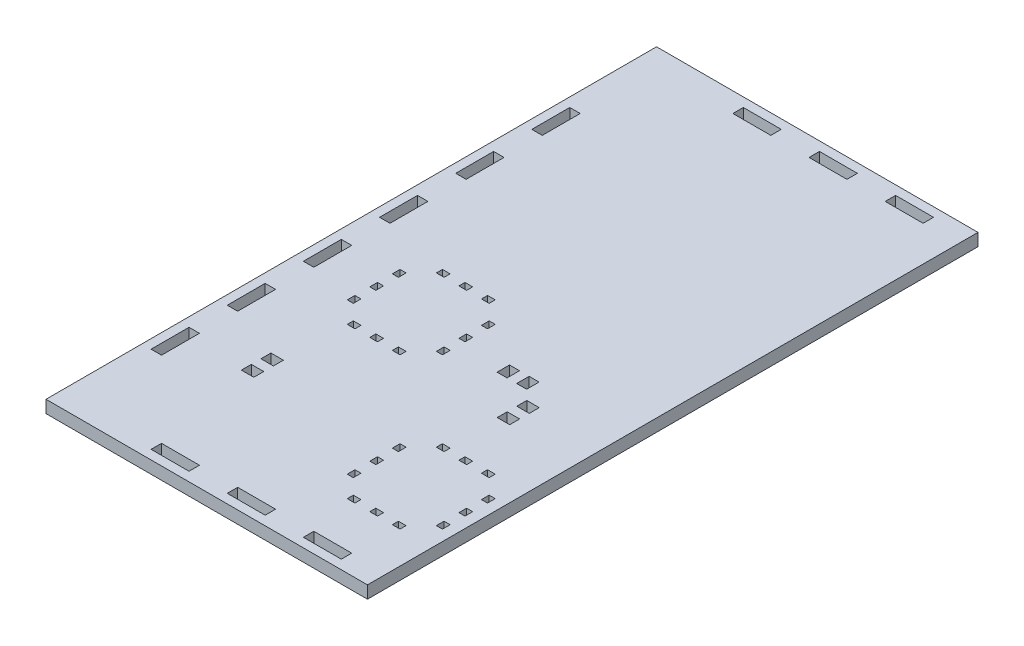
SolidWorks part; units mm, degrees
ref_plane "Front Plane" through (0, 0, 0) normal (0, 0, 1) x (1, 0, 0)
ref_plane "Top Plane" through (0, 0, 0) normal (0, 1, 0) x (1, 0, 0)
ref_plane "Right Plane" through (0, 0, 0) normal (1, 0, 0) x (0, 0, -1)
sketch "Sketch1" plane through (0, 0, 0) normal (0, 1, 0) x (1, 0, 0)
  line L182 (-7.5125, 303.9125) -> (303.8875, 303.9125)
  line L183 (-7.5125, 303.9125) -> (-7.5125, -7.4875)
  line L184 (-7.5125, -7.4875) -> (303.8875, -7.4875)
  line L185 (303.8875, 303.9125) -> (303.8875, -7.4875)
  line L195 (-2.9125, 60.7875) -> (2.4875, 60.7875)
  line L196 (-2.9125, 60.7875) -> (-2.9125, 41.3625)
  line L197 (-2.9125, 41.3625) -> (2.4875, 41.3625)
  line L198 (2.4875, 60.7875) -> (2.4875, 41.3625)
  line L200 (-2.9125, 99.6375) -> (2.4875, 99.6375)
  line L201 (-2.9125, 99.6375) -> (-2.9125, 80.2125)
  line L202 (-2.9125, 80.2125) -> (2.4875, 80.2125)
  line L203 (2.4875, 99.6375) -> (2.4875, 80.2125)
  line L205 (-2.9125, 138.4875) -> (2.4875, 138.4875)
  line L206 (-2.9125, 138.4875) -> (-2.9125, 119.0625)
  line L207 (-2.9125, 119.0625) -> (2.4875, 119.0625)
  line L208 (2.4875, 138.4875) -> (2.4875, 119.0625)
  line L211 (-2.9125, 177.3375) -> (2.4875, 177.3375)
  line L212 (-2.9125, 177.3375) -> (-2.9125, 157.9125)
  line L213 (-2.9125, 157.9125) -> (2.4875, 157.9125)
  line L214 (2.4875, 177.3375) -> (2.4875, 157.9125)
  line L216 (-2.9125, 216.1875) -> (2.4875, 216.1875)
  line L217 (-2.9125, 216.1875) -> (-2.9125, 196.7625)
  line L218 (-2.9125, 196.7625) -> (2.4875, 196.7625)
  line L219 (2.4875, 216.1875) -> (2.4875, 196.7625)
  line L221 (-2.9125, 255.0375) -> (2.4875, 255.0375)
  line L222 (-2.9125, 255.0375) -> (-2.9125, 235.6125)
  line L223 (-2.9125, 235.6125) -> (2.4875, 235.6125)
  line L224 (2.4875, 255.0375) -> (2.4875, 235.6125)
  line L236 (41.3625, 299.3125) -> (60.7875, 299.3125)
  line L237 (41.3625, 299.3125) -> (41.3625, 293.9125)
  line L238 (41.3625, 293.9125) -> (60.7875, 293.9125)
  line L239 (60.7875, 299.3125) -> (60.7875, 293.9125)
  line L241 (80.2125, 299.3125) -> (99.6375, 299.3125)
  line L242 (80.2125, 299.3125) -> (80.2125, 293.9125)
  line L243 (80.2125, 293.9125) -> (99.6375, 293.9125)
  line L244 (99.6375, 299.3125) -> (99.6375, 293.9125)
  line L246 (119.0625, 299.3125) -> (138.4875, 299.3125)
  line L247 (119.0625, 299.3125) -> (119.0625, 293.9125)
  line L248 (119.0625, 293.9125) -> (138.4875, 293.9125)
  line L249 (138.4875, 299.3125) -> (138.4875, 293.9125)
  line L251 (157.9125, 299.3125) -> (177.3375, 299.3125)
  line L252 (157.9125, 299.3125) -> (157.9125, 293.9125)
  line L253 (157.9125, 293.9125) -> (177.3375, 293.9125)
  line L254 (177.3375, 299.3125) -> (177.3375, 293.9125)
  line L256 (196.7625, 299.3125) -> (216.1875, 299.3125)
  line L257 (196.7625, 299.3125) -> (196.7625, 293.9125)
  line L258 (196.7625, 293.9125) -> (216.1875, 293.9125)
  line L259 (216.1875, 299.3125) -> (216.1875, 293.9125)
  line L260 (235.6125, 299.3125) -> (255.0375, 299.3125)
  line L261 (235.6125, 299.3125) -> (235.6125, 293.9125)
  line L262 (235.6125, 293.9125) -> (255.0375, 293.9125)
  line L263 (255.0375, 299.3125) -> (255.0375, 293.9125)
  line L272 (299.2875, 255.0625) -> (293.8875, 255.0625)
  line L273 (299.2875, 255.0625) -> (299.2875, 235.6375)
  line L274 (299.2875, 235.6375) -> (293.8875, 235.6375)
  line L275 (293.8875, 255.0625) -> (293.8875, 235.6375)
  line L276 (299.2875, 216.2125) -> (293.8875, 216.2125)
  line L277 (299.2875, 216.2125) -> (299.2875, 196.7875)
  line L278 (299.2875, 196.7875) -> (293.8875, 196.7875)
  line L279 (293.8875, 216.2125) -> (293.8875, 196.7875)
  line L280 (299.2875, 177.3625) -> (293.8875, 177.3625)
  line L281 (299.2875, 177.3625) -> (299.2875, 157.9375)
  line L282 (299.2875, 157.9375) -> (293.8875, 157.9375)
  line L283 (293.8875, 177.3625) -> (293.8875, 157.9375)
  line L284 (299.2875, 138.5125) -> (293.8875, 138.5125)
  line L285 (299.2875, 138.5125) -> (299.2875, 119.0875)
  line L286 (299.2875, 119.0875) -> (293.8875, 119.0875)
  line L287 (293.8875, 138.5125) -> (293.8875, 119.0875)
  line L288 (299.2875, 99.6625) -> (293.8875, 99.6625)
  line L289 (299.2875, 99.6625) -> (299.2875, 80.2375)
  line L290 (299.2875, 80.2375) -> (293.8875, 80.2375)
  line L291 (293.8875, 99.6625) -> (293.8875, 80.2375)
  line L292 (299.2875, 60.8125) -> (293.8875, 60.8125)
  line L293 (299.2875, 60.8125) -> (299.2875, 41.3875)
  line L294 (299.2875, 41.3875) -> (293.8875, 41.3875)
  line L295 (293.8875, 60.8125) -> (293.8875, 41.3875)
  line L304 (255.0125, 2.5125) -> (235.5875, 2.5125)
  line L305 (255.0125, 2.5125) -> (255.0125, -2.8875)
  line L306 (255.0125, -2.8875) -> (235.5875, -2.8875)
  line L307 (235.5875, 2.5125) -> (235.5875, -2.8875)
  line L308 (216.1625, 2.5125) -> (196.7375, 2.5125)
  line L309 (216.1625, 2.5125) -> (216.1625, -2.8875)
  line L310 (216.1625, -2.8875) -> (196.7375, -2.8875)
  line L311 (196.7375, 2.5125) -> (196.7375, -2.8875)
  line L312 (177.3125, 2.5125) -> (157.8875, 2.5125)
  line L313 (177.3125, 2.5125) -> (177.3125, -2.8875)
  line L314 (177.3125, -2.8875) -> (157.8875, -2.8875)
  line L315 (157.8875, 2.5125) -> (157.8875, -2.8875)
  line L316 (138.4625, 2.5125) -> (119.0375, 2.5125)
  line L317 (138.4625, 2.5125) -> (138.4625, -2.8875)
  line L318 (138.4625, -2.8875) -> (119.0375, -2.8875)
  line L319 (119.0375, 2.5125) -> (119.0375, -2.8875)
  line L320 (99.6125, 2.5125) -> (80.1875, 2.5125)
  line L321 (99.6125, 2.5125) -> (99.6125, -2.8875)
  line L322 (99.6125, -2.8875) -> (80.1875, -2.8875)
  line L323 (80.1875, 2.5125) -> (80.1875, -2.8875)
  line L324 (60.7625, 2.5125) -> (41.3375, 2.5125)
  line L325 (60.7625, 2.5125) -> (60.7625, -2.8875)
  line L326 (60.7625, -2.8875) -> (41.3375, -2.8875)
  line L327 (41.3375, 2.5125) -> (41.3375, -2.8875)
  line L528 (36.1625, 151.0125) -> (40.1625, 151.0125)
  line L529 (36.1625, 151.0125) -> (36.1625, 147.8375)
  line L530 (36.1625, 147.8375) -> (40.1625, 147.8375)
  line L531 (40.1625, 151.0125) -> (40.1625, 147.8375)
  line L532 (47.6625, 151.0125) -> (51.6625, 151.0125)
  line L533 (47.6625, 151.0125) -> (47.6625, 147.8375)
  line L534 (47.6625, 147.8375) -> (51.6625, 147.8375)
  line L535 (51.6625, 151.0125) -> (51.6625, 147.8375)
  line L536 (59.1625, 151.0125) -> (63.1625, 151.0125)
  line L537 (59.1625, 151.0125) -> (59.1625, 147.8375)
  line L538 (59.1625, 147.8375) -> (63.1625, 147.8375)
  line L539 (63.1625, 151.0125) -> (63.1625, 147.8375)
  line L540 (70.8125, 140.1875) -> (73.9875, 140.1875)
  line L541 (70.8125, 140.1875) -> (70.8125, 136.1875)
  line L542 (70.8125, 136.1875) -> (73.9875, 136.1875)
  line L543 (73.9875, 140.1875) -> (73.9875, 136.1875)
  line L544 (70.8125, 128.6875) -> (73.9875, 128.6875)
  line L545 (70.8125, 128.6875) -> (70.8125, 124.6875)
  line L546 (70.8125, 124.6875) -> (73.9875, 124.6875)
  line L547 (73.9875, 128.6875) -> (73.9875, 124.6875)
  line L548 (70.8125, 117.1875) -> (73.9875, 117.1875)
  line L549 (70.8125, 117.1875) -> (70.8125, 113.1875)
  line L550 (70.8125, 113.1875) -> (73.9875, 113.1875)
  line L551 (73.9875, 117.1875) -> (73.9875, 113.1875)
  line L552 (63.1625, 105.5375) -> (59.1625, 105.5375)
  line L553 (63.1625, 105.5375) -> (63.1625, 102.3625)
  line L554 (63.1625, 102.3625) -> (59.1625, 102.3625)
  line L555 (59.1625, 105.5375) -> (59.1625, 102.3625)
  line L556 (51.6625, 105.5375) -> (47.6625, 105.5375)
  line L557 (51.6625, 105.5375) -> (51.6625, 102.3625)
  line L558 (51.6625, 102.3625) -> (47.6625, 102.3625)
  line L559 (47.6625, 105.5375) -> (47.6625, 102.3625)
  line L560 (40.1625, 105.5375) -> (36.1625, 105.5375)
  line L561 (40.1625, 105.5375) -> (40.1625, 102.3625)
  line L562 (40.1625, 102.3625) -> (36.1625, 102.3625)
  line L563 (36.1625, 105.5375) -> (36.1625, 102.3625)
  line L564 (28.5125, 113.1875) -> (25.3375, 113.1875)
  line L565 (28.5125, 113.1875) -> (28.5125, 117.1875)
  line L566 (28.5125, 117.1875) -> (25.3375, 117.1875)
  line L567 (25.3375, 113.1875) -> (25.3375, 117.1875)
  line L568 (28.5125, 124.6875) -> (25.3375, 124.6875)
  line L569 (28.5125, 124.6875) -> (28.5125, 128.6875)
  line L570 (28.5125, 128.6875) -> (25.3375, 128.6875)
  line L571 (25.3375, 124.6875) -> (25.3375, 128.6875)
  line L572 (28.5125, 136.1875) -> (25.3375, 136.1875)
  line L573 (28.5125, 136.1875) -> (28.5125, 140.1875)
  line L574 (28.5125, 140.1875) -> (25.3375, 140.1875)
  line L575 (25.3375, 136.1875) -> (25.3375, 140.1875)
  line L576 (113.1625, 74.0125) -> (117.1625, 74.0125)
  line L577 (113.1625, 74.0125) -> (113.1625, 70.8375)
  line L578 (113.1625, 70.8375) -> (117.1625, 70.8375)
  line L579 (117.1625, 74.0125) -> (117.1625, 70.8375)
  line L580 (124.6625, 74.0125) -> (128.6625, 74.0125)
  line L581 (124.6625, 74.0125) -> (124.6625, 70.8375)
  line L582 (124.6625, 70.8375) -> (128.6625, 70.8375)
  line L583 (128.6625, 74.0125) -> (128.6625, 70.8375)
  line L584 (136.1625, 74.0125) -> (140.1625, 74.0125)
  line L585 (136.1625, 74.0125) -> (136.1625, 70.8375)
  line L586 (136.1625, 70.8375) -> (140.1625, 70.8375)
  line L587 (140.1625, 74.0125) -> (140.1625, 70.8375)
  line L588 (150.9875, 63.1875) -> (147.8125, 63.1875)
  line L589 (150.9875, 63.1875) -> (150.9875, 59.1875)
  line L590 (150.9875, 59.1875) -> (147.8125, 59.1875)
  line L591 (147.8125, 63.1875) -> (147.8125, 59.1875)
  line L592 (150.9875, 51.6875) -> (147.8125, 51.6875)
  line L593 (150.9875, 51.6875) -> (150.9875, 47.6875)
  line L594 (150.9875, 47.6875) -> (147.8125, 47.6875)
  line L595 (147.8125, 51.6875) -> (147.8125, 47.6875)
  line L596 (150.9875, 40.1875) -> (147.8125, 40.1875)
  line L597 (150.9875, 40.1875) -> (150.9875, 36.1875)
  line L598 (150.9875, 36.1875) -> (147.8125, 36.1875)
  line L599 (147.8125, 40.1875) -> (147.8125, 36.1875)
  line L600 (140.1625, 28.5375) -> (136.1625, 28.5375)
  line L601 (140.1625, 28.5375) -> (140.1625, 25.3625)
  line L602 (140.1625, 25.3625) -> (136.1625, 25.3625)
  line L603 (136.1625, 28.5375) -> (136.1625, 25.3625)
  line L604 (128.6625, 28.5375) -> (124.6625, 28.5375)
  line L605 (128.6625, 28.5375) -> (128.6625, 25.3625)
  line L606 (128.6625, 25.3625) -> (124.6625, 25.3625)
  line L607 (124.6625, 28.5375) -> (124.6625, 25.3625)
  line L608 (117.1625, 28.5375) -> (113.1625, 28.5375)
  line L609 (117.1625, 28.5375) -> (117.1625, 25.3625)
  line L610 (117.1625, 25.3625) -> (113.1625, 25.3625)
  line L611 (113.1625, 28.5375) -> (113.1625, 25.3625)
  line L612 (105.5125, 36.1875) -> (102.3375, 36.1875)
  line L613 (105.5125, 36.1875) -> (105.5125, 40.1875)
  line L614 (105.5125, 40.1875) -> (102.3375, 40.1875)
  line L615 (102.3375, 36.1875) -> (102.3375, 40.1875)
  line L616 (105.5125, 47.6875) -> (102.3375, 47.6875)
  line L617 (105.5125, 47.6875) -> (105.5125, 51.6875)
  line L618 (105.5125, 51.6875) -> (102.3375, 51.6875)
  line L619 (102.3375, 47.6875) -> (102.3375, 51.6875)
  line L620 (105.5125, 59.1875) -> (102.3375, 59.1875)
  line L621 (105.5125, 59.1875) -> (105.5125, 63.1875)
  line L622 (105.5125, 63.1875) -> (102.3375, 63.1875)
  line L623 (102.3375, 59.1875) -> (102.3375, 63.1875)
  dimension "D1" = 311.4
  dimension "D3" = 311.4
extrude "Boss-Extrude4" add sketch "Sketch1" along normal blind 6.35
sketch "Sketch4" plane through (0, 6.35, 0) normal (0, 1, 0) x (1, 0, 0)
  line L0 (303.8875, 303.9125) -> (-7.5125, 303.9125) construction
  line B0 (41.3375, 2.5125) -> (60.7625, 2.5125)
  line B1 (2.4875, 2.5125) -> (21.9125, 2.5125)
  line B2 (2.4875, 2.5125) -> (2.4875, -2.8875)
  line B3 (2.4875, -2.8875) -> (21.9125, -2.8875)
  line B4 (21.9125, 2.5125) -> (21.9125, -2.8875)
  line B5 (41.3375, 2.5125) -> (41.3375, -2.8875)
  line B6 (41.3375, -2.8875) -> (60.7625, -2.8875)
  line B7 (60.7625, 2.5125) -> (60.7625, -2.8875)
  line B8 (80.1875, 2.5125) -> (99.6125, 2.5125)
  line B9 (80.1875, 2.5125) -> (80.1875, -2.8875)
  line B10 (80.1875, -2.8875) -> (99.6125, -2.8875)
  line B11 (99.6125, 2.5125) -> (99.6125, -2.8875)
  line B12 (119.0375, 2.5125) -> (138.4625, 2.5125)
  line B13 (119.0375, 2.5125) -> (119.0375, -2.8875)
  line B14 (119.0375, -2.8875) -> (138.4625, -2.8875)
  line B15 (138.4625, 2.5125) -> (138.4625, -2.8875)
  line B16 (157.8875, 2.5125) -> (177.3125, 2.5125)
  line B17 (157.8875, 2.5125) -> (157.8875, -2.8875)
  line B18 (157.8875, -2.8875) -> (177.3125, -2.8875)
  line B19 (177.3125, 2.5125) -> (177.3125, -2.8875)
  line B20 (196.7375, 2.5125) -> (216.1625, 2.5125)
  line B21 (196.7375, 2.5125) -> (196.7375, -2.8875)
  line B22 (196.7375, -2.8875) -> (216.1625, -2.8875)
  line B23 (216.1625, 2.5125) -> (216.1625, -2.8875)
  line B24 (235.5875, 2.5125) -> (255.0125, 2.5125)
  line B25 (235.5875, 2.5125) -> (235.5875, -2.8875)
  line B26 (235.5875, -2.8875) -> (255.0125, -2.8875)
  line B27 (255.0125, 2.5125) -> (255.0125, -2.8875)
  line B28 (274.4375, 2.5125) -> (293.8625, 2.5125)
  line B29 (274.4375, 2.5125) -> (274.4375, -2.8875)
  line B30 (274.4375, -2.8875) -> (293.8625, -2.8875)
  line B31 (293.8625, 2.5125) -> (293.8625, -2.8875)
  line B32 (-2.9125, 60.7875) -> (2.4875, 60.7875)
  line B33 (-2.9125, 2.5125) -> (2.4875, 2.5125)
  line B34 (-2.9125, 2.5125) -> (-2.9125, 21.9375)
  line B35 (-2.9125, 21.9375) -> (2.4875, 21.9375)
  line B36 (2.4875, 2.5125) -> (2.4875, 21.9375)
  line B37 (2.4875, 41.3625) -> (2.4875, 60.7875)
  line B38 (-2.9125, 41.3625) -> (-2.9125, 60.7875)
  line B39 (-2.9125, 41.3625) -> (2.4875, 41.3625)
  line B40 (-2.9125, 99.6375) -> (2.4875, 99.6375)
  line B41 (2.4875, 80.2125) -> (2.4875, 99.6375)
  line B42 (-2.9125, 80.2125) -> (-2.9125, 99.6375)
  line B43 (-2.9125, 80.2125) -> (2.4875, 80.2125)
  line B44 (-2.9125, 138.4875) -> (2.4875, 138.4875)
  line B45 (2.4875, 119.0625) -> (2.4875, 138.4875)
  line B46 (-2.9125, 119.0625) -> (-2.9125, 138.4875)
  line B47 (-2.9125, 119.0625) -> (2.4875, 119.0625)
  line B48 (-2.9125, 177.3375) -> (2.4875, 177.3375)
  line B49 (2.4875, 157.9125) -> (2.4875, 177.3375)
  line B50 (-2.9125, 157.9125) -> (-2.9125, 177.3375)
  line B51 (-2.9125, 157.9125) -> (2.4875, 157.9125)
  line B52 (-2.9125, 216.1875) -> (2.4875, 216.1875)
  line B53 (2.4875, 196.7625) -> (2.4875, 216.1875)
  line B54 (-2.9125, 196.7625) -> (-2.9125, 216.1875)
  line B55 (-2.9125, 196.7625) -> (2.4875, 196.7625)
  line B56 (-2.9125, 255.0375) -> (2.4875, 255.0375)
  line B57 (2.4875, 235.6125) -> (2.4875, 255.0375)
  line B58 (-2.9125, 235.6125) -> (-2.9125, 255.0375)
  line B59 (-2.9125, 235.6125) -> (2.4875, 235.6125)
  line B60 (-2.9125, 293.8875) -> (2.4875, 293.8875)
  line B61 (2.4875, 274.4625) -> (2.4875, 293.8875)
  line B62 (-2.9125, 274.4625) -> (-2.9125, 293.8875)
  line B63 (-2.9125, 274.4625) -> (2.4875, 274.4625)
  line B64 (-7.5125, 303.9125) -> (303.8875, -7.4875) construction
  line B65 (21.9375, 299.3125) -> (21.9375, 293.9125)
  line B66 (21.9375, 299.3125) -> (2.5125, 299.3125)
  line B67 (21.9375, 293.9125) -> (2.5125, 293.9125)
  line B68 (2.5125, 299.3125) -> (2.5125, 293.9125)
  line B69 (60.7875, 299.3125) -> (60.7875, 293.9125)
  line B70 (60.7875, 299.3125) -> (41.3625, 299.3125)
  line B71 (60.7875, 293.9125) -> (41.3625, 293.9125)
  line B72 (41.3625, 299.3125) -> (41.3625, 293.9125)
  line B73 (99.6375, 299.3125) -> (99.6375, 293.9125)
  line B74 (99.6375, 299.3125) -> (80.2125, 299.3125)
  line B75 (99.6375, 293.9125) -> (80.2125, 293.9125)
  line B76 (80.2125, 299.3125) -> (80.2125, 293.9125)
  line B77 (138.4875, 299.3125) -> (138.4875, 293.9125)
  line B78 (138.4875, 299.3125) -> (119.0625, 299.3125)
  line B79 (138.4875, 293.9125) -> (119.0625, 293.9125)
  line B80 (119.0625, 299.3125) -> (119.0625, 293.9125)
  line B81 (177.3375, 299.3125) -> (177.3375, 293.9125)
  line B82 (177.3375, 299.3125) -> (157.9125, 299.3125)
  line B83 (177.3375, 293.9125) -> (157.9125, 293.9125)
  line B84 (157.9125, 299.3125) -> (157.9125, 293.9125)
  line B85 (216.1875, 299.3125) -> (216.1875, 293.9125)
  line B86 (216.1875, 299.3125) -> (196.7625, 299.3125)
  line B87 (216.1875, 293.9125) -> (196.7625, 293.9125)
  line B88 (196.7625, 299.3125) -> (196.7625, 293.9125)
  line B89 (255.0375, 299.3125) -> (255.0375, 293.9125)
  line B90 (255.0375, 299.3125) -> (235.6125, 299.3125)
  line B91 (255.0375, 293.9125) -> (235.6125, 293.9125)
  line B92 (293.8875, 293.9125) -> (274.4625, 293.9125)
  line B93 (274.4625, 299.3125) -> (274.4625, 293.9125)
  line B94 (293.8875, 299.3125) -> (274.4625, 299.3125)
  line B95 (293.8875, 299.3125) -> (293.8875, 293.9125)
  line B96 (235.6125, 299.3125) -> (235.6125, 293.9125)
  line B97 (293.8875, 2.5375) -> (299.2875, 2.5375)
  line B98 (299.2875, 21.9625) -> (299.2875, 2.5375)
  line B99 (293.8875, 21.9625) -> (299.2875, 21.9625)
  line B100 (293.8875, 21.9625) -> (293.8875, 2.5375)
  line B101 (293.8875, 41.3875) -> (299.2875, 41.3875)
  line B102 (299.2875, 60.8125) -> (299.2875, 41.3875)
  line B103 (293.8875, 60.8125) -> (299.2875, 60.8125)
  line B104 (293.8875, 60.8125) -> (293.8875, 41.3875)
  line B105 (293.8875, 80.2375) -> (299.2875, 80.2375)
  line B106 (299.2875, 99.6625) -> (299.2875, 80.2375)
  line B107 (293.8875, 99.6625) -> (299.2875, 99.6625)
  line B108 (293.8875, 99.6625) -> (293.8875, 80.2375)
  line B109 (293.8875, 119.0875) -> (299.2875, 119.0875)
  line B110 (299.2875, 138.5125) -> (299.2875, 119.0875)
  line B111 (293.8875, 138.5125) -> (299.2875, 138.5125)
  line B112 (293.8875, 138.5125) -> (293.8875, 119.0875)
  line B113 (293.8875, 157.9375) -> (299.2875, 157.9375)
  line B114 (299.2875, 177.3625) -> (299.2875, 157.9375)
  line B115 (293.8875, 177.3625) -> (299.2875, 177.3625)
  line B116 (293.8875, 177.3625) -> (293.8875, 157.9375)
  line B117 (293.8875, 196.7875) -> (299.2875, 196.7875)
  line B118 (299.2875, 216.2125) -> (299.2875, 196.7875)
  line B119 (293.8875, 216.2125) -> (299.2875, 216.2125)
  line B120 (293.8875, 216.2125) -> (293.8875, 196.7875)
  line B121 (293.8875, 235.6375) -> (299.2875, 235.6375)
  line B122 (299.2875, 255.0625) -> (299.2875, 235.6375)
  line B123 (293.8875, 255.0625) -> (299.2875, 255.0625)
  line B124 (293.8875, 274.4875) -> (299.2875, 274.4875)
  line B125 (299.2875, 293.9125) -> (299.2875, 274.4875)
  line B126 (293.8875, 293.9125) -> (299.2875, 293.9125)
  line B127 (293.8875, 293.9125) -> (293.8875, 274.4875)
  line B128 (293.8875, 255.0625) -> (293.8875, 235.6375)
  line B129 (2.5125, 293.9125) -> (2.4875, 293.8875)
  line B130 (293.8875, 2.5375) -> (293.8625, 2.5125)
  line B131 (35.6625, 260.7375) -> (115.6625, 260.7375)
  line B132 (35.6625, 260.7375) -> (35.6625, 180.7375)
  line B133 (35.6625, 180.7375) -> (115.6625, 180.7375)
  line B134 (115.6625, 260.7375) -> (115.6625, 180.7375)
  arc B135 (-2.9125, 293.8875) -> (2.5125, 299.2874) centre (2.4875, 293.8875) cw
  arc B136 (293.8625, -2.8875) -> (299.2624, 2.5375) centre (293.8625, 2.5125) ccw
  arc B137 (299.2875, 293.9125) -> (293.8875, 299.3125) centre (293.8875, 293.9125) ccw
  arc B138 (2.4875, -2.8875) -> (-2.9125, 2.5125) centre (2.4875, 2.5125) cw
sketch_block_instance "Outer Mounting Holes-4"
sketch_block "Outer Mounting Holes" parameters "D1"=5.4, "D2"=19.425, "D3"=19.425, "D4"=19.425, "D5"=80, "D6"=302.2
extrude "Cut-Extrude3" cut sketch "Sketch4" against normal blind 6.35 contours B66 B68 B67 B65 | B62 B63 B61 B60 | B135 B60 B129 B68 | B126 B137 B95 | B95 B94 B93 B92 | B126 B127 B124 B125 | B33 B36 B35 B34 | B4 B1 B2 B3 | B138 B2 B33 | B31 B136 B97 B130 | B31 B28 B29 B30 | B99 B100 B97 B98
sketch "Sketch5" plane through (0, 6.35, 0) normal (0, 1, 0) x (1, 0, 0)
  line L8 (254.9969, 293.9531) -> (254.9969, 299.2719)
  line L9 (235.6531, 293.9531) -> (254.9969, 293.9531)
  line L10 (235.6531, 299.2719) -> (235.6531, 293.9531)
  line L11 (254.9969, 299.2719) -> (235.6531, 299.2719)
  line L12 (254.9969, 293.9531) -> (254.9969, 299.2719)
  line L13 (235.6531, 293.9531) -> (254.9969, 293.9531)
  line L14 (235.6531, 299.2719) -> (235.6531, 293.9531)
  line L15 (254.9969, 299.2719) -> (235.6531, 299.2719)
  line L16 (-7.5531, -7.5281) -> (303.9281, -7.5281)
  line L17 (303.9281, -7.5281) -> (303.9281, 303.9531)
  line L18 (-7.5531, 303.9531) -> (-7.5531, -7.5281)
  line L19 (303.9281, 303.9531) -> (-7.5531, 303.9531)
  line L20 (-7.5531, -7.5281) -> (303.9281, -7.5281)
  line L21 (303.9281, -7.5281) -> (303.9281, 303.9531)
  line L22 (-7.5531, 303.9531) -> (-7.5531, -7.5281)
  line L23 (303.9281, 303.9531) -> (-7.5531, 303.9531)
  line L24 (293.8625, -2.8469) -> (274.4781, -2.8469)
  line L25 (274.4781, -2.8469) -> (274.4781, 2.4719)
  line L26 (274.4781, 2.4719) -> (293.8625, 2.4719)
  line L27 (293.8625, -2.8469) -> (274.4781, -2.8469)
  line L28 (274.5031, 299.2719) -> (293.8875, 299.2719)
  line L29 (274.5031, 293.9531) -> (274.5031, 299.2719)
  line L30 (293.8875, 293.9531) -> (274.5031, 293.9531)
  line L31 (274.5031, 299.2719) -> (293.8875, 299.2719)
  line L32 (274.5031, 293.9531) -> (274.5031, 299.2719)
  line L33 (293.8875, 293.9531) -> (274.5031, 293.9531)
  line L34 (299.2469, 41.4281) -> (299.2469, 60.7719)
  line L35 (293.9281, 196.8281) -> (299.2469, 196.8281)
  line L36 (293.9281, 216.1719) -> (293.9281, 196.8281)
  line L37 (299.2469, 196.8281) -> (299.2469, 216.1719)
  line L38 (299.2469, 216.1719) -> (293.9281, 216.1719)
  line L39 (293.9281, 196.8281) -> (299.2469, 196.8281)
  line L40 (293.9281, 274.5281) -> (299.2469, 274.5281)
  line L41 (299.2469, 274.5281) -> (299.2469, 293.9125)
  line L42 (293.9281, 293.9125) -> (293.9281, 274.5281)
  line L43 (293.9281, 274.5281) -> (299.2469, 274.5281)
  line L44 (299.2469, 274.5281) -> (299.2469, 293.9125)
  line L45 (293.9281, 293.9125) -> (293.9281, 274.5281)
  line L46 (293.9281, 216.1719) -> (293.9281, 196.8281)
  line L47 (299.2469, 196.8281) -> (299.2469, 216.1719)
  line L48 (299.2469, 216.1719) -> (293.9281, 216.1719)
  line L49 (293.9281, 41.4281) -> (299.2469, 41.4281)
  line L50 (293.9281, 60.7719) -> (293.9281, 41.4281)
  line L51 (299.2469, 60.7719) -> (293.9281, 60.7719)
  line L52 (299.2469, 41.4281) -> (299.2469, 60.7719)
  line L53 (293.9281, 41.4281) -> (299.2469, 41.4281)
  line L54 (293.9281, 60.7719) -> (293.9281, 41.4281)
  line L55 (299.2469, 60.7719) -> (293.9281, 60.7719)
  line L56 (274.4781, -2.8469) -> (274.4781, 2.4719)
  line L57 (293.9281, 235.6781) -> (299.2469, 235.6781)
  line L58 (299.2469, 235.6781) -> (299.2469, 255.0219)
  line L59 (299.2469, 255.0219) -> (293.9281, 255.0219)
  line L60 (293.9281, 255.0219) -> (293.9281, 235.6781)
  line L61 (293.9281, 235.6781) -> (299.2469, 235.6781)
  line L62 (299.2469, 235.6781) -> (299.2469, 255.0219)
  line L63 (299.2469, 255.0219) -> (293.9281, 255.0219)
  line L64 (293.9281, 255.0219) -> (293.9281, 235.6781)
  line L65 (274.4781, 2.4719) -> (293.8625, 2.4719)
  line L70 (299.2469, 157.9781) -> (299.2469, 177.3219)
  line L71 (293.9281, 177.3219) -> (293.9281, 157.9781)
  line L72 (293.9281, 157.9781) -> (299.2469, 157.9781)
  line L73 (21.8969, 293.9531) -> (21.8969, 299.2719)
  line L74 (2.5125, 293.9531) -> (21.8969, 293.9531)
  line L75 (21.8969, 299.2719) -> (2.5125, 299.2719)
  line L76 (21.8969, 293.9531) -> (21.8969, 299.2719)
  line L77 (2.5125, 293.9531) -> (21.8969, 293.9531)
  line L78 (21.8969, 299.2719) -> (2.5125, 299.2719)
  line L79 (299.2469, 177.3219) -> (293.9281, 177.3219)
  line L80 (299.2469, 157.9781) -> (299.2469, 177.3219)
  line L81 (293.9281, 177.3219) -> (293.9281, 157.9781)
  line L82 (293.9281, 157.9781) -> (299.2469, 157.9781)
  line L83 (299.2469, 177.3219) -> (293.9281, 177.3219)
  line L85 (-2.8719, 274.5031) -> (2.4469, 274.5031)
  line L86 (-2.8719, 293.8875) -> (-2.8719, 274.5031)
  line L87 (2.4469, 274.5031) -> (2.4469, 293.8875)
  line L88 (-2.8719, 274.5031) -> (2.4469, 274.5031)
  line L89 (-2.8719, 293.8875) -> (-2.8719, 274.5031)
  line L90 (2.4469, 274.5031) -> (2.4469, 293.8875)
  line L91 (-2.8719, 157.9531) -> (2.4469, 157.9531)
  line L92 (216.1219, -2.8469) -> (216.1219, 2.4719)
  line L93 (-2.8719, 177.2969) -> (-2.8719, 157.9531)
  line L94 (196.7781, 2.4719) -> (196.7781, -2.8469)
  line L95 (196.7781, -2.8469) -> (216.1219, -2.8469)
  line L96 (216.1219, 2.4719) -> (196.7781, 2.4719)
  line L97 (254.9719, -2.8469) -> (254.9719, 2.4719)
  line L98 (235.6281, 2.4719) -> (235.6281, -2.8469)
  line L99 (235.6281, -2.8469) -> (254.9719, -2.8469)
  line L100 (299.2469, 119.1281) -> (299.2469, 138.4719)
  line L101 (293.9281, 138.4719) -> (293.9281, 119.1281)
  line L102 (60.7469, 293.9531) -> (60.7469, 299.2719)
  line L103 (41.4031, 293.9531) -> (60.7469, 293.9531)
  line L104 (41.4031, 299.2719) -> (41.4031, 293.9531)
  line L105 (60.7469, 299.2719) -> (41.4031, 299.2719)
  line L106 (60.7469, 293.9531) -> (60.7469, 299.2719)
  line L107 (41.4031, 293.9531) -> (60.7469, 293.9531)
  line L108 (41.4031, 299.2719) -> (41.4031, 293.9531)
  line L109 (60.7469, 299.2719) -> (41.4031, 299.2719)
  line L110 (293.9281, 119.1281) -> (299.2469, 119.1281)
  line L111 (299.2469, 138.4719) -> (293.9281, 138.4719)
  line L112 (299.2469, 119.1281) -> (299.2469, 138.4719)
  line L113 (293.9281, 138.4719) -> (293.9281, 119.1281)
  line L114 (293.9281, 119.1281) -> (299.2469, 119.1281)
  line L115 (299.2469, 138.4719) -> (293.9281, 138.4719)
  line L116 (254.9719, 2.4719) -> (235.6281, 2.4719)
  line L117 (254.9719, -2.8469) -> (254.9719, 2.4719)
  line L118 (235.6281, 2.4719) -> (235.6281, -2.8469)
  line L119 (235.6281, -2.8469) -> (254.9719, -2.8469)
  line L120 (254.9719, 2.4719) -> (235.6281, 2.4719)
  line L121 (216.1219, -2.8469) -> (216.1219, 2.4719)
  line L122 (196.7781, 2.4719) -> (196.7781, -2.8469)
  line L123 (196.7781, -2.8469) -> (216.1219, -2.8469)
  line L124 (99.5969, 293.9531) -> (99.5969, 299.2719)
  line L125 (80.2531, 299.2719) -> (80.2531, 293.9531)
  line L126 (80.2531, 293.9531) -> (99.5969, 293.9531)
  line L127 (99.5969, 299.2719) -> (80.2531, 299.2719)
  line L128 (99.5969, 293.9531) -> (99.5969, 299.2719)
  line L129 (80.2531, 299.2719) -> (80.2531, 293.9531)
  line L130 (80.2531, 293.9531) -> (99.5969, 293.9531)
  line L131 (99.5969, 299.2719) -> (80.2531, 299.2719)
  line L132 (216.1219, 2.4719) -> (196.7781, 2.4719)
  line L133 (2.4469, 157.9531) -> (2.4469, 177.2969)
  line L134 (299.2469, 80.2781) -> (299.2469, 99.6219)
  line L135 (293.9281, 80.2781) -> (299.2469, 80.2781)
  line L136 (293.9281, 99.6219) -> (293.9281, 80.2781)
  line L137 (299.2469, 99.6219) -> (293.9281, 99.6219)
  line L138 (299.2469, 80.2781) -> (299.2469, 99.6219)
  line L139 (293.9281, 80.2781) -> (299.2469, 80.2781)
  line L140 (293.9281, 99.6219) -> (293.9281, 80.2781)
  line L141 (299.2469, 99.6219) -> (293.9281, 99.6219)
  line L142 (119.1031, 299.2719) -> (119.1031, 293.9531)
  line L143 (138.4469, 293.9531) -> (138.4469, 299.2719)
  line L144 (119.1031, 293.9531) -> (138.4469, 293.9531)
  line L145 (138.4469, 299.2719) -> (119.1031, 299.2719)
  line L146 (119.1031, 299.2719) -> (119.1031, 293.9531)
  line L147 (138.4469, 293.9531) -> (138.4469, 299.2719)
  line L148 (119.1031, 293.9531) -> (138.4469, 293.9531)
  line L149 (138.4469, 299.2719) -> (119.1031, 299.2719)
  line L150 (2.4469, 177.2969) -> (-2.8719, 177.2969)
  line L151 (-2.8719, 157.9531) -> (2.4469, 157.9531)
  line L152 (-2.8719, 177.2969) -> (-2.8719, 157.9531)
  line L153 (2.4469, 157.9531) -> (2.4469, 177.2969)
  line L154 (2.4469, 177.2969) -> (-2.8719, 177.2969)
  line L155 (-2.8719, 235.6531) -> (2.4469, 235.6531)
  line L156 (2.4469, 235.6531) -> (2.4469, 254.9969)
  line L157 (-2.8719, 254.9969) -> (-2.8719, 235.6531)
  line L158 (2.4469, 254.9969) -> (-2.8719, 254.9969)
  line L159 (177.2719, -2.8469) -> (177.2719, 2.4719)
  line L160 (157.9531, 299.2719) -> (157.9531, 293.9531)
  line L161 (177.2969, 293.9531) -> (177.2969, 299.2719)
  line L162 (157.9531, 293.9531) -> (177.2969, 293.9531)
  line L163 (177.2969, 299.2719) -> (157.9531, 299.2719)
  line L164 (157.9531, 299.2719) -> (157.9531, 293.9531)
  line L165 (177.2969, 293.9531) -> (177.2969, 299.2719)
  line L166 (157.9531, 293.9531) -> (177.2969, 293.9531)
  line L167 (177.2969, 299.2719) -> (157.9531, 299.2719)
  line L168 (157.9281, 2.4719) -> (157.9281, -2.8469)
  line L169 (157.9281, -2.8469) -> (177.2719, -2.8469)
  line L170 (299.2469, 2.5375) -> (299.2469, 21.9219)
  line L171 (299.2469, 21.9219) -> (293.9281, 21.9219)
  line L172 (293.9281, 21.9219) -> (293.9281, 2.5375)
  line L173 (299.2469, 2.5375) -> (299.2469, 21.9219)
  line L174 (299.2469, 21.9219) -> (293.9281, 21.9219)
  line L175 (293.9281, 21.9219) -> (293.9281, 2.5375)
  line L176 (177.2719, 2.4719) -> (157.9281, 2.4719)
  line L177 (177.2719, -2.8469) -> (177.2719, 2.4719)
  line L178 (157.9281, 2.4719) -> (157.9281, -2.8469)
  line L179 (157.9281, -2.8469) -> (177.2719, -2.8469)
  line L180 (196.8031, 299.2719) -> (196.8031, 293.9531)
  line L181 (216.1469, 293.9531) -> (216.1469, 299.2719)
  line L182 (216.1469, 299.2719) -> (196.8031, 299.2719)
  line L183 (196.8031, 293.9531) -> (216.1469, 293.9531)
  line L184 (196.8031, 299.2719) -> (196.8031, 293.9531)
  line L185 (216.1469, 293.9531) -> (216.1469, 299.2719)
  line L186 (216.1469, 299.2719) -> (196.8031, 299.2719)
  line L187 (196.8031, 293.9531) -> (216.1469, 293.9531)
  line L188 (177.2719, 2.4719) -> (157.9281, 2.4719)
  line L189 (-2.8719, 235.6531) -> (2.4469, 235.6531)
  line L190 (2.4469, 235.6531) -> (2.4469, 254.9969)
  line L194 (-2.8719, 254.9969) -> (-2.8719, 235.6531)
  line L195 (-2.8719, 196.8031) -> (2.4469, 196.8031)
  line L196 (2.4469, 196.8031) -> (2.4469, 216.1469)
  line L197 (-2.8719, 216.1469) -> (-2.8719, 196.8031)
  line L198 (2.4469, 216.1469) -> (-2.8719, 216.1469)
  line L199 (138.4219, 2.4719) -> (119.0781, 2.4719)
  line L200 (119.0781, -2.8469) -> (138.4219, -2.8469)
  line L201 (138.4219, -2.8469) -> (138.4219, 2.4719)
  line L202 (119.0781, 2.4719) -> (119.0781, -2.8469)
  line L203 (138.4219, 2.4719) -> (119.0781, 2.4719)
  line L204 (119.0781, -2.8469) -> (138.4219, -2.8469)
  line L205 (138.4219, -2.8469) -> (138.4219, 2.4719)
  line L206 (119.0781, 2.4719) -> (119.0781, -2.8469)
  line L207 (-2.8719, 196.8031) -> (2.4469, 196.8031)
  line L208 (2.4469, 196.8031) -> (2.4469, 216.1469)
  line L209 (-2.8719, 216.1469) -> (-2.8719, 196.8031)
  line L210 (2.4469, 216.1469) -> (-2.8719, 216.1469)
  line L211 (2.4469, 254.9969) -> (-2.8719, 254.9969)
  line L212 (51.6219, 147.8781) -> (51.6219, 150.9719)
  line L213 (47.7031, 147.8781) -> (51.6219, 147.8781)
  line L214 (47.7031, 150.9719) -> (47.7031, 147.8781)
  line L215 (51.6219, 150.9719) -> (47.7031, 150.9719)
  line L216 (51.6219, 147.8781) -> (51.6219, 150.9719)
  line L217 (80.2281, 2.4719) -> (80.2281, -2.8469)
  line L218 (99.5719, -2.8469) -> (99.5719, 2.4719)
  line L219 (80.2281, -2.8469) -> (99.5719, -2.8469)
  line L220 (99.5719, 2.4719) -> (80.2281, 2.4719)
  line L221 (80.2281, 2.4719) -> (80.2281, -2.8469)
  line L222 (99.5719, -2.8469) -> (99.5719, 2.4719)
  line L223 (80.2281, -2.8469) -> (99.5719, -2.8469)
  line L224 (99.5719, 2.4719) -> (80.2281, 2.4719)
  line L225 (47.7031, 147.8781) -> (51.6219, 147.8781)
  line L226 (47.7031, 150.9719) -> (47.7031, 147.8781)
  line L227 (51.6219, 150.9719) -> (47.7031, 150.9719)
  line L228 (63.1219, 147.8781) -> (63.1219, 150.9719)
  line L229 (59.2031, 147.8781) -> (63.1219, 147.8781)
  line L230 (59.2031, 150.9719) -> (59.2031, 147.8781)
  line L231 (63.1219, 150.9719) -> (59.2031, 150.9719)
  line L232 (63.1219, 147.8781) -> (63.1219, 150.9719)
  line L233 (59.2031, 147.8781) -> (63.1219, 147.8781)
  line L234 (59.2031, 150.9719) -> (59.2031, 147.8781)
  line L235 (41.3781, 2.4719) -> (41.3781, -2.8469)
  line L236 (60.7219, -2.8469) -> (60.7219, 2.4719)
  line L237 (41.3781, -2.8469) -> (60.7219, -2.8469)
  line L238 (60.7219, 2.4719) -> (41.3781, 2.4719)
  line L239 (41.3781, 2.4719) -> (41.3781, -2.8469)
  line L240 (60.7219, -2.8469) -> (60.7219, 2.4719)
  line L241 (41.3781, -2.8469) -> (60.7219, -2.8469)
  line L242 (60.7219, 2.4719) -> (41.3781, 2.4719)
  line L243 (63.1219, 150.9719) -> (59.2031, 150.9719)
  line L248 (21.8719, 2.4719) -> (21.8719, -2.8469)
  line L249 (21.8719, -2.8469) -> (2.4875, -2.8469)
  line L250 (2.4875, 2.4719) -> (21.8719, 2.4719)
  line L251 (21.8719, 2.4719) -> (21.8719, -2.8469)
  line L252 (21.8719, -2.8469) -> (2.4875, -2.8469)
  line L253 (2.4875, 2.4719) -> (21.8719, 2.4719)
  line L260 (2.4469, 21.8969) -> (2.4469, 2.5125)
  line L261 (-2.8719, 2.5125) -> (-2.8719, 21.8969)
  line L262 (-2.8719, 21.8969) -> (2.4469, 21.8969)
  line L263 (2.4469, 21.8969) -> (2.4469, 2.5125)
  line L264 (-2.8719, 2.5125) -> (-2.8719, 21.8969)
  line L265 (-2.8719, 21.8969) -> (2.4469, 21.8969)
  line L266 (40.1219, 147.8781) -> (40.1219, 150.9719)
  line L267 (36.2031, 147.8781) -> (40.1219, 147.8781)
  line L268 (36.2031, 150.9719) -> (36.2031, 147.8781)
  line L269 (40.1219, 150.9719) -> (36.2031, 150.9719)
  line L270 (40.1219, 147.8781) -> (40.1219, 150.9719)
  line L271 (36.2031, 147.8781) -> (40.1219, 147.8781)
  line L272 (36.2031, 150.9719) -> (36.2031, 147.8781)
  line L273 (40.1219, 150.9719) -> (36.2031, 150.9719)
  line L277 (-2.8719, 41.4031) -> (2.4469, 41.4031)
  line L278 (2.4469, 41.4031) -> (2.4469, 60.7469)
  line L279 (-2.8719, 60.7469) -> (-2.8719, 41.4031)
  line L280 (2.4469, 60.7469) -> (-2.8719, 60.7469)
  line L281 (-2.8719, 41.4031) -> (2.4469, 41.4031)
  line L282 (2.4469, 41.4031) -> (2.4469, 60.7469)
  line L283 (-2.8719, 60.7469) -> (-2.8719, 41.4031)
  line L284 (2.4469, 60.7469) -> (-2.8719, 60.7469)
  line L292 (28.4719, 136.2281) -> (28.4719, 140.1469)
  line L293 (25.3781, 140.1469) -> (25.3781, 136.2281)
  line L294 (25.3781, 136.2281) -> (28.4719, 136.2281)
  line L295 (-2.8719, 80.2531) -> (2.4469, 80.2531)
  line L296 (-2.8719, 99.5969) -> (-2.8719, 80.2531)
  line L297 (2.4469, 80.2531) -> (2.4469, 99.5969)
  line L298 (2.4469, 99.5969) -> (-2.8719, 99.5969)
  line L299 (-2.8719, 80.2531) -> (2.4469, 80.2531)
  line L300 (-2.8719, 99.5969) -> (-2.8719, 80.2531)
  line L301 (2.4469, 80.2531) -> (2.4469, 99.5969)
  line L302 (2.4469, 99.5969) -> (-2.8719, 99.5969)
  line L303 (28.4719, 140.1469) -> (25.3781, 140.1469)
  line L304 (28.4719, 136.2281) -> (28.4719, 140.1469)
  line L305 (25.3781, 140.1469) -> (25.3781, 136.2281)
  line L306 (25.3781, 136.2281) -> (28.4719, 136.2281)
  line L307 (28.4719, 140.1469) -> (25.3781, 140.1469)
  line L313 (-2.8719, 119.1031) -> (2.4469, 119.1031)
  line L314 (2.4469, 119.1031) -> (2.4469, 138.4469)
  line L315 (-2.8719, 138.4469) -> (-2.8719, 119.1031)
  line L316 (2.4469, 138.4469) -> (-2.8719, 138.4469)
  line L317 (-2.8719, 119.1031) -> (2.4469, 119.1031)
  line L318 (2.4469, 119.1031) -> (2.4469, 138.4469)
  line L319 (-2.8719, 138.4469) -> (-2.8719, 119.1031)
  line L320 (2.4469, 138.4469) -> (-2.8719, 138.4469)
  line L326 (28.4719, 124.7281) -> (28.4719, 128.6469)
  line L327 (25.3781, 128.6469) -> (25.3781, 124.7281)
  line L328 (25.3781, 124.7281) -> (28.4719, 124.7281)
  line L329 (28.4719, 128.6469) -> (25.3781, 128.6469)
  line L330 (28.4719, 124.7281) -> (28.4719, 128.6469)
  line L331 (25.3781, 128.6469) -> (25.3781, 124.7281)
  line L332 (25.3781, 124.7281) -> (28.4719, 124.7281)
  line L333 (28.4719, 128.6469) -> (25.3781, 128.6469)
  line L344 (28.4719, 113.2281) -> (28.4719, 117.1469)
  line L345 (25.3781, 117.1469) -> (25.3781, 113.2281)
  line L346 (25.3781, 113.2281) -> (28.4719, 113.2281)
  line L347 (28.4719, 117.1469) -> (25.3781, 117.1469)
  line L348 (28.4719, 113.2281) -> (28.4719, 117.1469)
  line L349 (25.3781, 117.1469) -> (25.3781, 113.2281)
  line L350 (25.3781, 113.2281) -> (28.4719, 113.2281)
  line L351 (28.4719, 117.1469) -> (25.3781, 117.1469)
  line L362 (40.1219, 102.4031) -> (40.1219, 105.4969)
  line L363 (36.2031, 105.4969) -> (36.2031, 102.4031)
  line L364 (36.2031, 102.4031) -> (40.1219, 102.4031)
  line L365 (40.1219, 105.4969) -> (36.2031, 105.4969)
  line L366 (40.1219, 102.4031) -> (40.1219, 105.4969)
  line L367 (36.2031, 105.4969) -> (36.2031, 102.4031)
  line L368 (36.2031, 102.4031) -> (40.1219, 102.4031)
  line L369 (40.1219, 105.4969) -> (36.2031, 105.4969)
  line L380 (51.6219, 102.4031) -> (51.6219, 105.4969)
  line L381 (47.7031, 105.4969) -> (47.7031, 102.4031)
  line L382 (51.6219, 105.4969) -> (47.7031, 105.4969)
  line L383 (47.7031, 102.4031) -> (51.6219, 102.4031)
  line L384 (51.6219, 102.4031) -> (51.6219, 105.4969)
  line L385 (47.7031, 105.4969) -> (47.7031, 102.4031)
  line L386 (51.6219, 105.4969) -> (47.7031, 105.4969)
  line L387 (47.7031, 102.4031) -> (51.6219, 102.4031)
  line L398 (63.1219, 102.4031) -> (63.1219, 105.4969)
  line L399 (59.2031, 105.4969) -> (59.2031, 102.4031)
  line L400 (59.2031, 102.4031) -> (63.1219, 102.4031)
  line L401 (63.1219, 105.4969) -> (59.2031, 105.4969)
  line L402 (63.1219, 102.4031) -> (63.1219, 105.4969)
  line L403 (59.2031, 105.4969) -> (59.2031, 102.4031)
  line L404 (59.2031, 102.4031) -> (63.1219, 102.4031)
  line L405 (63.1219, 105.4969) -> (59.2031, 105.4969)
  line L416 (73.9469, 136.2281) -> (73.9469, 140.1469)
  line L417 (70.8531, 136.2281) -> (73.9469, 136.2281)
  line L418 (70.8531, 140.1469) -> (70.8531, 136.2281)
  line L419 (73.9469, 140.1469) -> (70.8531, 140.1469)
  line L420 (73.9469, 136.2281) -> (73.9469, 140.1469)
  line L421 (70.8531, 136.2281) -> (73.9469, 136.2281)
  line L422 (70.8531, 140.1469) -> (70.8531, 136.2281)
  line L423 (73.9469, 140.1469) -> (70.8531, 140.1469)
  line L434 (73.9469, 124.7281) -> (73.9469, 128.6469)
  line L435 (70.8531, 124.7281) -> (73.9469, 124.7281)
  line L436 (70.8531, 128.6469) -> (70.8531, 124.7281)
  line L437 (73.9469, 128.6469) -> (70.8531, 128.6469)
  line L438 (73.9469, 124.7281) -> (73.9469, 128.6469)
  line L439 (70.8531, 124.7281) -> (73.9469, 124.7281)
  line L440 (70.8531, 128.6469) -> (70.8531, 124.7281)
  line L441 (73.9469, 128.6469) -> (70.8531, 128.6469)
  line L456 (73.9469, 113.2281) -> (73.9469, 117.1469)
  line L457 (70.8531, 113.2281) -> (73.9469, 113.2281)
  line L458 (70.8531, 117.1469) -> (70.8531, 113.2281)
  line L459 (73.9469, 117.1469) -> (70.8531, 117.1469)
  line L460 (73.9469, 113.2281) -> (73.9469, 117.1469)
  line L461 (70.8531, 113.2281) -> (73.9469, 113.2281)
  line L462 (70.8531, 117.1469) -> (70.8531, 113.2281)
  line L463 (73.9469, 117.1469) -> (70.8531, 117.1469)
  line L474 (128.6219, 70.8781) -> (128.6219, 73.9719)
  line L475 (124.7031, 73.9719) -> (124.7031, 70.8781)
  line L476 (124.7031, 70.8781) -> (128.6219, 70.8781)
  line L477 (128.6219, 73.9719) -> (124.7031, 73.9719)
  line L478 (128.6219, 70.8781) -> (128.6219, 73.9719)
  line L479 (124.7031, 73.9719) -> (124.7031, 70.8781)
  line L480 (124.7031, 70.8781) -> (128.6219, 70.8781)
  line L481 (128.6219, 73.9719) -> (124.7031, 73.9719)
  line L492 (113.2031, 73.9719) -> (113.2031, 70.8781)
  line L493 (117.1219, 70.8781) -> (117.1219, 73.9719)
  line L494 (113.2031, 70.8781) -> (117.1219, 70.8781)
  line L495 (117.1219, 73.9719) -> (113.2031, 73.9719)
  line L496 (113.2031, 73.9719) -> (113.2031, 70.8781)
  line L497 (117.1219, 70.8781) -> (117.1219, 73.9719)
  line L498 (113.2031, 70.8781) -> (117.1219, 70.8781)
  line L499 (117.1219, 73.9719) -> (113.2031, 73.9719)
  line L510 (140.1219, 70.8781) -> (140.1219, 73.9719)
  line L511 (136.2031, 73.9719) -> (136.2031, 70.8781)
  line L512 (136.2031, 70.8781) -> (140.1219, 70.8781)
  line L513 (140.1219, 73.9719) -> (136.2031, 73.9719)
  line L514 (140.1219, 70.8781) -> (140.1219, 73.9719)
  line L515 (136.2031, 73.9719) -> (136.2031, 70.8781)
  line L516 (136.2031, 70.8781) -> (140.1219, 70.8781)
  line L517 (140.1219, 73.9719) -> (136.2031, 73.9719)
  line L528 (150.9469, 59.2281) -> (150.9469, 63.1469)
  line L529 (147.8531, 63.1469) -> (147.8531, 59.2281)
  line L530 (147.8531, 59.2281) -> (150.9469, 59.2281)
  line L531 (150.9469, 63.1469) -> (147.8531, 63.1469)
  line L532 (150.9469, 59.2281) -> (150.9469, 63.1469)
  line L533 (147.8531, 63.1469) -> (147.8531, 59.2281)
  line L534 (147.8531, 59.2281) -> (150.9469, 59.2281)
  line L535 (150.9469, 63.1469) -> (147.8531, 63.1469)
  line L546 (150.9469, 47.7281) -> (150.9469, 51.6469)
  line L547 (147.8531, 51.6469) -> (147.8531, 47.7281)
  line L548 (147.8531, 47.7281) -> (150.9469, 47.7281)
  line L549 (150.9469, 51.6469) -> (147.8531, 51.6469)
  line L550 (150.9469, 47.7281) -> (150.9469, 51.6469)
  line L551 (147.8531, 51.6469) -> (147.8531, 47.7281)
  line L552 (147.8531, 47.7281) -> (150.9469, 47.7281)
  line L553 (150.9469, 51.6469) -> (147.8531, 51.6469)
  line L564 (147.8531, 40.1469) -> (147.8531, 36.2281)
  line L565 (150.9469, 36.2281) -> (150.9469, 40.1469)
  line L566 (147.8531, 36.2281) -> (150.9469, 36.2281)
  line L567 (150.9469, 40.1469) -> (147.8531, 40.1469)
  line L568 (147.8531, 40.1469) -> (147.8531, 36.2281)
  line L569 (150.9469, 36.2281) -> (150.9469, 40.1469)
  line L570 (147.8531, 36.2281) -> (150.9469, 36.2281)
  line L571 (150.9469, 40.1469) -> (147.8531, 40.1469)
  line L582 (140.1219, 25.4031) -> (140.1219, 28.4969)
  line L583 (136.2031, 25.4031) -> (140.1219, 25.4031)
  line L584 (136.2031, 28.4969) -> (136.2031, 25.4031)
  line L585 (140.1219, 28.4969) -> (136.2031, 28.4969)
  line L586 (140.1219, 25.4031) -> (140.1219, 28.4969)
  line L587 (136.2031, 25.4031) -> (140.1219, 25.4031)
  line L588 (136.2031, 28.4969) -> (136.2031, 25.4031)
  line L589 (140.1219, 28.4969) -> (136.2031, 28.4969)
  line L600 (128.6219, 25.4031) -> (128.6219, 28.4969)
  line L601 (124.7031, 28.4969) -> (124.7031, 25.4031)
  line L602 (124.7031, 25.4031) -> (128.6219, 25.4031)
  line L603 (128.6219, 28.4969) -> (124.7031, 28.4969)
  line L604 (128.6219, 25.4031) -> (128.6219, 28.4969)
  line L605 (124.7031, 28.4969) -> (124.7031, 25.4031)
  line L606 (124.7031, 25.4031) -> (128.6219, 25.4031)
  line L607 (128.6219, 28.4969) -> (124.7031, 28.4969)
  line L618 (113.2031, 28.4969) -> (113.2031, 25.4031)
  line L619 (117.1219, 25.4031) -> (117.1219, 28.4969)
  line L620 (113.2031, 25.4031) -> (117.1219, 25.4031)
  line L621 (117.1219, 28.4969) -> (113.2031, 28.4969)
  line L622 (113.2031, 28.4969) -> (113.2031, 25.4031)
  line L623 (117.1219, 25.4031) -> (117.1219, 28.4969)
  line L624 (113.2031, 25.4031) -> (117.1219, 25.4031)
  line L625 (117.1219, 28.4969) -> (113.2031, 28.4969)
  line L636 (105.4719, 36.2281) -> (105.4719, 40.1469)
  line L637 (102.3781, 40.1469) -> (102.3781, 36.2281)
  line L638 (102.3781, 36.2281) -> (105.4719, 36.2281)
  line L639 (105.4719, 40.1469) -> (102.3781, 40.1469)
  line L640 (105.4719, 36.2281) -> (105.4719, 40.1469)
  line L641 (102.3781, 40.1469) -> (102.3781, 36.2281)
  line L642 (102.3781, 36.2281) -> (105.4719, 36.2281)
  line L643 (105.4719, 40.1469) -> (102.3781, 40.1469)
  line L654 (102.3781, 51.6469) -> (102.3781, 47.7281)
  line L655 (105.4719, 47.7281) -> (105.4719, 51.6469)
  line L656 (102.3781, 47.7281) -> (105.4719, 47.7281)
  line L657 (105.4719, 51.6469) -> (102.3781, 51.6469)
  line L658 (102.3781, 51.6469) -> (102.3781, 47.7281)
  line L659 (105.4719, 47.7281) -> (105.4719, 51.6469)
  line L660 (102.3781, 47.7281) -> (105.4719, 47.7281)
  line L661 (105.4719, 51.6469) -> (102.3781, 51.6469)
  line L672 (105.4719, 59.2281) -> (105.4719, 63.1469)
  line L673 (102.3781, 63.1469) -> (102.3781, 59.2281)
  line L674 (102.3781, 59.2281) -> (105.4719, 59.2281)
  line L675 (105.4719, 63.1469) -> (102.3781, 63.1469)
  line L676 (105.4719, 59.2281) -> (105.4719, 63.1469)
  line L677 (102.3781, 63.1469) -> (102.3781, 59.2281)
  line L678 (102.3781, 59.2281) -> (105.4719, 59.2281)
  line L679 (105.4719, 63.1469) -> (102.3781, 63.1469)
  arc A2 (299.2469, 293.9125) -> (293.8875, 299.2719) centre (293.8875, 293.9125) ccw
  arc A3 (299.2469, 293.9125) -> (293.8875, 299.2719) centre (293.8875, 293.9125) ccw
  arc A4 (293.8625, -2.8469) -> (299.2218, 2.5373) centre (293.8625, 2.5125) ccw
  arc A5 (293.8625, -2.8469) -> (299.2218, 2.5373) centre (293.8625, 2.5125) ccw
  arc A6 (-2.8719, 2.5125) -> (2.4875, -2.8469) centre (2.4875, 2.5125) ccw
  arc A7 (-2.8719, 2.5125) -> (2.4875, -2.8469) centre (2.4875, 2.5125) ccw
  arc A11 (2.5123, 299.2468) -> (-2.8719, 293.8875) centre (2.4875, 293.8875) ccw
  arc A12 (2.5123, 299.2468) -> (-2.8719, 293.8875) centre (2.4875, 293.8875) ccw
  dimension "D1" = 0.0406
  dimension "D2" = 0.0406
  dimension "D3" = 0.0406
  dimension "D4" = 0.0406
  dimension "D5" = 0.0406
  dimension "D6" = 0.0406
  dimension "D7" = 0.0406
  dimension "D8" = 0.0406
  dimension "D9" = 0.0406
  dimension "D10" = 0.0406
  dimension "D11" = 0.0406
  dimension "D12" = 0.0406
  dimension "D13" = 0.0406
  dimension "D14" = 0.0406
  dimension "D15" = 0.0406
  dimension "D16" = 0.0406
  dimension "D17" = 0.0406
  dimension "D18" = 0.0406
  dimension "D19" = 0.0406
  dimension "D20" = 0.0406
  dimension "D21" = 0.0406
  dimension "D22" = 0.0406
  dimension "D23" = 0.0406
  dimension "D24" = 0.0406
  dimension "D25" = 0.0406
  dimension "D26" = 0.0406
  dimension "D27" = 0.0406
  dimension "D28" = 0.0406
  dimension "D29" = 0.0406
  dimension "D30" = 0.0406
  dimension "D31" = 0.0406
  dimension "D32" = 0.0406
  dimension "D33" = 0.0406
  dimension "D34" = 0.0406
  dimension "D35" = 0.0406
  dimension "D36" = 0.0406
  dimension "D37" = 0.0406
  dimension "D38" = 0.0406
  dimension "D39" = 0.0406
  dimension "D40" = 0.0406
  dimension "D41" = 0.0406
  dimension "D42" = 0.0406
  dimension "D43" = 0.0406
  dimension "D44" = 0.0406
  dimension "D45" = 0.0406
  dimension "D46" = 0.0406
  dimension "D47" = 0.0406
  dimension "D48" = 0.0406
  dimension "D49" = 0.0406
  dimension "D50" = 0.0406
  dimension "D51" = 0.0406
  dimension "D52" = 0.0406
  dimension "D53" = 0.0406
  dimension "D54" = 0.0406
  dimension "D55" = 0.0406
  dimension "D56" = 0.0406
  dimension "D57" = 0.0406
  dimension "D58" = 0.0406
  dimension "D59" = 0.0406
  dimension "D60" = 0.0406
  dimension "D61" = 0.0406
extrude "Boss-Extrude5" add sketch "Sketch5" against normal blind 6.35
sketch "Sketch7" plane through (0, 0, 0) normal (0, -1, 0) x (1, 0, 0)
  line L0 (-7.5531, 7.5281) -> (303.9281, 7.5281) construction
  line L1 (35.7438, -55.1988) -> (29.3938, -55.1988)
  line L2 (35.7438, -55.1988) -> (35.7438, -60.2801)
  line L3 (35.7438, -60.2801) -> (29.3938, -60.2801)
  line L4 (29.3938, -55.1988) -> (29.3938, -60.2801)
  line L5 (-7.5531, -303.9531) -> (-7.5531, 7.5281) construction
  line L6 (110.6219, -119.5058) -> (110.6219, -114.5871) construction
  line L7 (35.7438, -65.1988) -> (29.3938, -65.1988)
  line L8 (35.7438, -65.1988) -> (35.7438, -70.2801)
  line L9 (35.7438, -70.2801) -> (29.3938, -70.2801)
  line L10 (29.3938, -65.1988) -> (29.3938, -70.2801)
  line L11 (115.6219, -99.5058) -> (121.9719, -99.5058)
  line L12 (115.6219, -99.5058) -> (115.6219, -104.5871)
  line L13 (115.6219, -104.5871) -> (121.9719, -104.5871)
  line L14 (121.9719, -99.5058) -> (121.9719, -104.5871)
  line L15 (115.6219, -109.5058) -> (121.9719, -109.5058)
  line L16 (115.6219, -109.5058) -> (115.6219, -114.5871)
  line L17 (115.6219, -114.5871) -> (121.9719, -114.5871)
  line L18 (121.9719, -109.5058) -> (121.9719, -114.5871)
  line L19 (110.6219, -119.5058) -> (105.5406, -119.5058)
  line L20 (110.6219, -119.5058) -> (110.6219, -125.8558)
  line L21 (110.6219, -125.8558) -> (105.5406, -125.8558)
  line L22 (105.5406, -119.5058) -> (105.5406, -125.8558)
  line L23 (100.6219, -119.5058) -> (95.5406, -119.5058)
  line L24 (100.6219, -119.5058) -> (100.6219, -125.8558)
  line L25 (100.6219, -125.8558) -> (95.5406, -125.8558)
  line L26 (95.5406, -119.5058) -> (95.5406, -125.8558)
  line L27 (110.6219, -114.5871) -> (115.6219, -114.5871) construction
  line L28 (115.6219, -109.5058) -> (115.6219, -104.5871) construction
  line L29 (105.5406, -119.5058) -> (100.6219, -119.5058) construction
  point P28 (110.6219, -114.5871)
  dimension "D1" = 62.727
  dimension "D2" = 36.9469
  dimension "D3" = 6.35
  dimension "D4" = 5.0813
  dimension "D5" = 4.9187
  dimension "D6" = 4.9187
  dimension "D7" = 4.9187
  dimension "D8" = 103.0937
  dimension "D9" = 4.9187
  dimension "D10" = 5
extrude "Cut-Extrude4" cut sketch "Sketch7" against normal up to surface (6.35 mm away) up to face at (103.925, 6.35, -61.1875)
sketch "Sketch8" plane through (0, 0, 0) normal (0, -1, 0) x (1, 0, 0)
  line L5 (156.4469, -303.9531) -> (156.4469, 7.5281)
  line L6 (-7.5531, 7.5281) -> (303.9281, 7.5281) construction
  line L7 (156.4469, 7.5281) -> (303.9281, 7.5281)
  line L8 (303.9281, 7.5281) -> (303.9281, -303.9531)
  line L9 (303.9281, -303.9531) -> (156.4469, -303.9531)
  dimension "D1" = 164
extrude "Cut-Extrude5" cut sketch "Sketch8" against normal up to surface (6.35 mm away) up to face at (32.5688, 6.35, -57.7395)
equation "\"stepper width\"=4.23"
equation "\"stepper hole disctance\"= 3.1"
equation "\"stepper hole diameter\"=0.34"
equation "\"stepper shaft hole\"=2.4"
equation "\"tooth width\"=0.4"
equation "\"tooth thickness\"=0.3175"
equation "\"tooth to side\"=0.75"
equation "\"motor chamber height\"= 6"
equation "\"enclosure length\"= 22 + 6"
equation "\"platform diameter\"= 9"
equation "\"teeth width\"=0.3175"
equation "\"teeth lenght\"=2"
equation "\"tower width\"=7.7"
equation "\"support width\"=1"
equation "\"trial hole spacing\"= 0.75"
equation "\"mounting distance\"= 4"
equation "\"half belt distance\"=5.5"
equation "\"holder distance to wall\"= 2.25"
equation "\"bearing outer diameter\"= 1.6"
equation "\"half belt length\"=5.5"
equation "\"screw hole diameter\"=0.351"
equation "\"distance between screw hles\"=3"
equation "\"spinner to stack center to center\"= 15"
equation "\"stack to elevator center to center\"=20"
equation "\"elevator to wall\"=3.5"
equation "\"D1\"= \"tooth width\""
equation "\"D2\"= \"tooth thickness\""
equation "\"D3\"= \"tooth to side\""
equation "\"D1@Elevator Platform Block\"=\"motor width\""
equation "\"D2@Elevator Platform Block\"=\"motor width\""
equation "\"D3@Elevator Platform Block\"=\"motor width\""
equation "\"D1@Elevator Platform Block\"=\"elevator width\""
equation "\"D2@Elevator Platform Block\"=\"elevator width\""
equation "\"D3@Elevator Platform Block\"=\"drivign screw diameter\""
equation "\"D1@Block1\"=\"tooth width\""
equation "\"D2@Block1\"=\"tooth thickness\""
equation "\"D3@Block1\"=\"tooth to side\""
equation "\"D31@Sketch1\"=\"teeth lenght\""
equation "\"D32@Sketch1\"=\"tooth thickness\""
equation "\"D1\" = \"tooth width\""
equation "\"D2\" = \"tooth thickness\""
equation "\"D3\" = \"tooth to side\""
equation "\"D4\" = \"tooth to side\""
equation "\"D14@Sketch1\"=\"holder distance to wall\""
equation "\"D5@Sketch1\"=\"teeth lenght\""
equation "\"D2@Sketch1\"=\"teeth width\""
equation "\"D15@Sketch1\"=\"stack to elevator center to center\""
equation "\"D1\" = \"tooth thickness\""
equation "\"D12@Sketch1\"=\"stack to elevator center to center\"/2"
equation "\"D11@Sketch1\"=\"spinner to stack center to center\"/2"
equation "\"D10@Sketch1\"=\"holder distance to wall\""
equation "\"D13@Sketch1\"=\"spinner to stack center to center\""
equation "\"D1\" = \"motor width\""
equation "\"D1\" = \"elevator width\""
equation "\"D3\" = \"drivign screw diameter\""
equation "\"D3\" = \"motor width\""
equation "\"D2\" = \"elevator width\""
equation "\"D2\" = \"motor width\""
equation "\"D10@Sketch1\"=\"elevator to wall\""
equation "\"D11@Sketch1\"=\"elevator to wall\""
